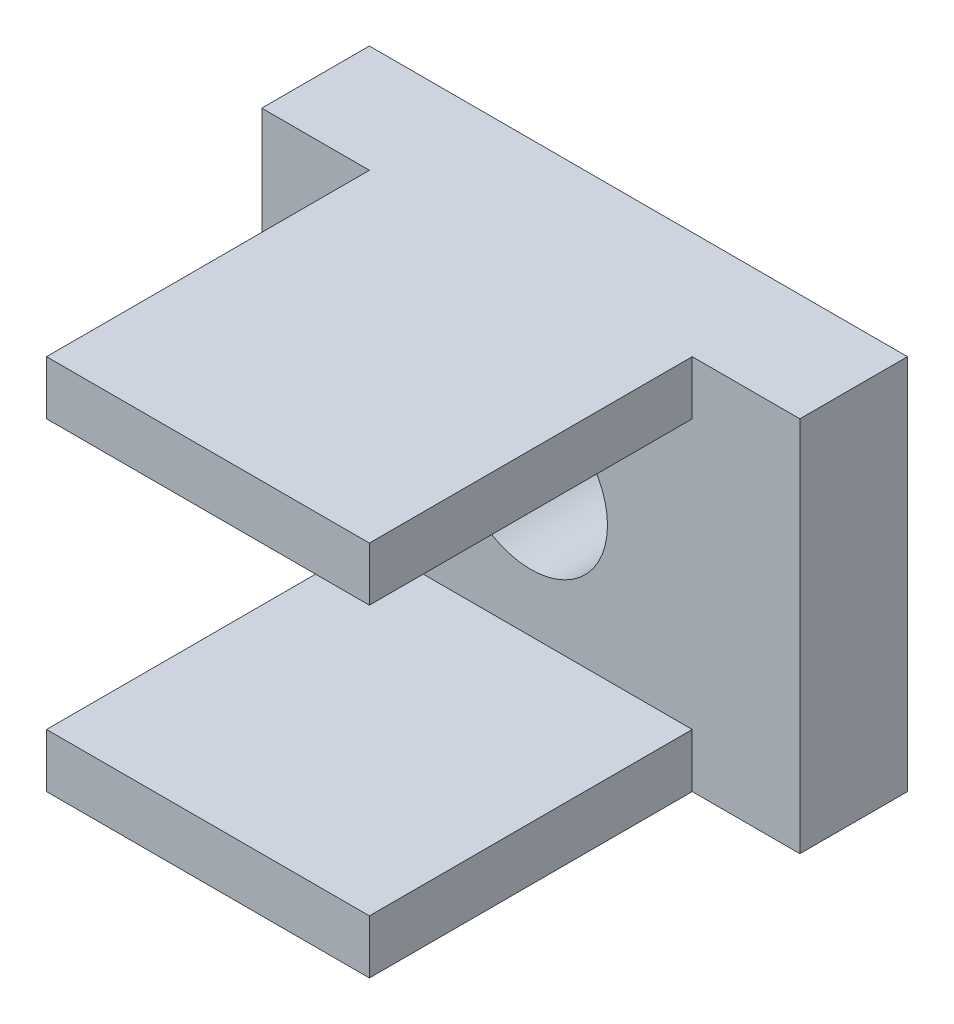
SolidWorks part; units mm, degrees
ref_plane "Front Plane" through (0, 0, 0) normal (0, 0, 1) x (1, 0, 0)
ref_plane "Top Plane" through (0, 0, 0) normal (0, 1, 0) x (1, 0, 0)
ref_plane "Right Plane" through (0, 0, 0) normal (1, 0, 0) x (0, 0, -1)
sketch "Sketch1" plane through (0, 0, 0) normal (0, 0, 1) x (1, 0, 0)
  line L1 (5, -3.5) -> (-5, -3.5)
  line L2 (5, -3.5) -> (5, 3.5)
  line L3 (5, 3.5) -> (-5, 3.5)
  line L4 (-5, -3.5) -> (-5, 3.5)
  line L5 (5, -3.5) -> (-5, 3.5) construction
  line L6 (5, 3.5) -> (-5, -3.5) construction
  circle A0 centre (0, 0) radius 1.425
  point P0 (0, 0)
  dimension "D3" = 2.85
  dimension "D1" = 10
  dimension "D2" = 7
extrude "Boss-Extrude1" add sketch "Sketch1" along normal blind 2
sketch "Sketch3" plane through (0, 0, 2) normal (0, 0, 1) x (1, 0, 0)
  line L0 (5, 3.5) -> (-5, 3.5) construction
  line L1 (3, 2.5) -> (-3, 2.5)
  line L2 (3, 2.5) -> (3, 3.5)
  line L3 (3, 3.5) -> (-3, 3.5)
  line L4 (-3, 2.5) -> (-3, 3.5)
  line L5 (3, 2.5) -> (-3, 3.5) construction
  line L6 (3, 3.5) -> (-3, 2.5) construction
  point P0 (0, 3)
  dimension "D1" = 6
  dimension "D2" = 1
extrude "Boss-Extrude2" add sketch "Sketch3" along normal blind 6
mirror "Mirror1" about plane through (0, 0, 0) normal (0, 1, 0) of "Boss-Extrude2"
